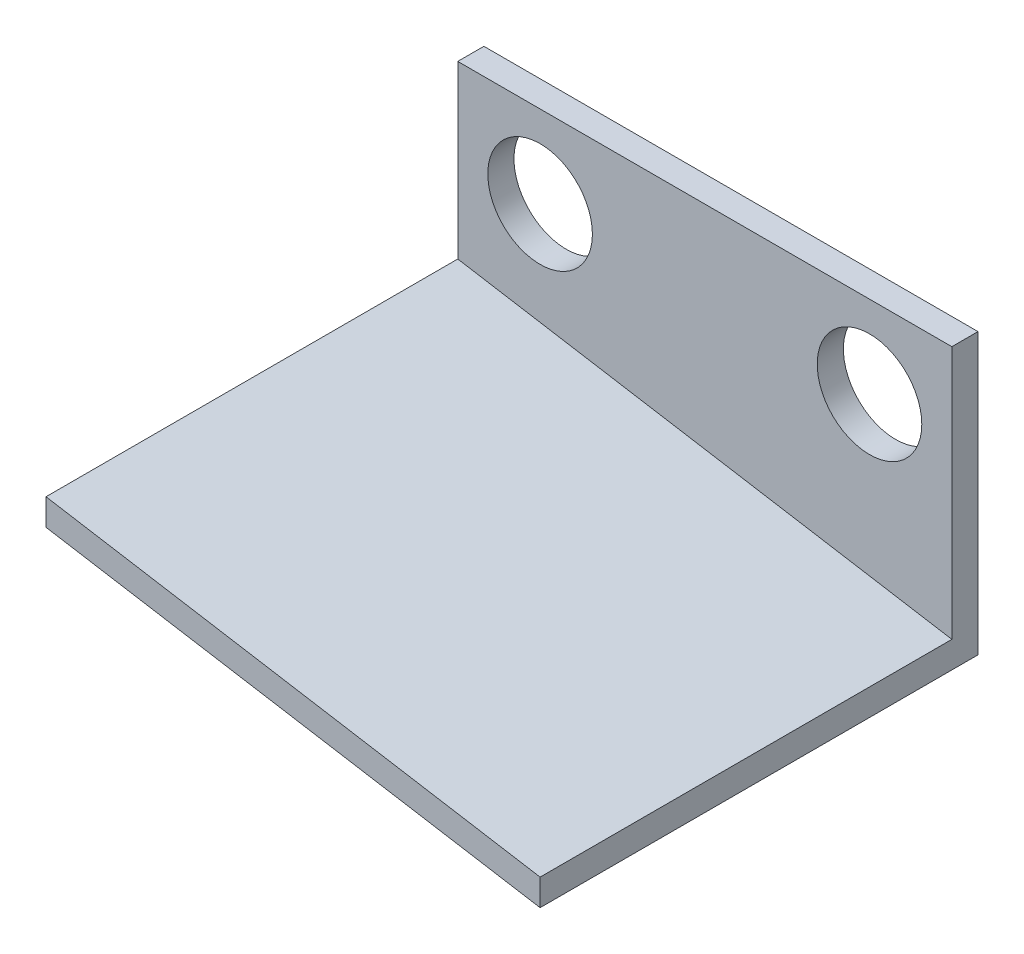
SolidWorks part; units mm, degrees
ref_plane "Alzado" through (0, 0, 0) normal (0, 0, 1) x (1, 0, 0)
ref_plane "Planta" through (0, 0, 0) normal (0, 1, 0) x (1, 0, 0)
ref_plane "Vista lateral" through (0, 0, 0) normal (1, 0, 0) x (0, 0, -1)
sketch "Croquis3" plane through (0, 0, 0) normal (0, 0, 1) x (1, 0, 0)
  line L0 (-15, 0) -> (-15, -17) construction
  line L1 (0, 0) -> (-30, 0)
  line L2 (0, 0) -> (0, -17)
  line L3 (0, -17) -> (-30, -17)
  line L4 (-30, 0) -> (-30, -17)
  line L5 (0, -17) -> (-30, -12)
  circle A1 centre (-5, -5) radius 3.175
  circle A2 centre (-25, -5) radius 3.175
  point P9 (-5.7169, -4.9964)
  point P10 (-5.3124, -7.4233)
  point P11 (-25, -5.4807)
  point P14 (-25, -5.0218)
  dimension "D7" = 6.35
  dimension "D1" = 20
  dimension "D2" = 12
  dimension "D3" = 7
  dimension "D4" = 5
  dimension "D5" = 5
  dimension "D6" = 5
extrude "Saliente-Extruir2" add sketch "Croquis3" along normal blind 1.5875 contours L0 L1 L4 L5 A2 | L1 L0 L5 L2 A1
sketch "Croquis4" plane through (0, 0, 1.5875) normal (0, 0, 1) x (1, 0, 0)
  line L0 (-30, -12) -> (0, -17)
  line L1 (0, -17) -> (0, -15.3906)
  line L2 (0, 0) -> (0, -17) construction
  line L3 (0, -15.3906) -> (-30, -10.3906)
  line L4 (-30, 0) -> (-30, -12) construction
  line L5 (-30, -10.3906) -> (-30, -12)
  dimension "D1" = 1.5875
extrude "Saliente-Extruir3" add sketch "Croquis4" along normal blind 25
